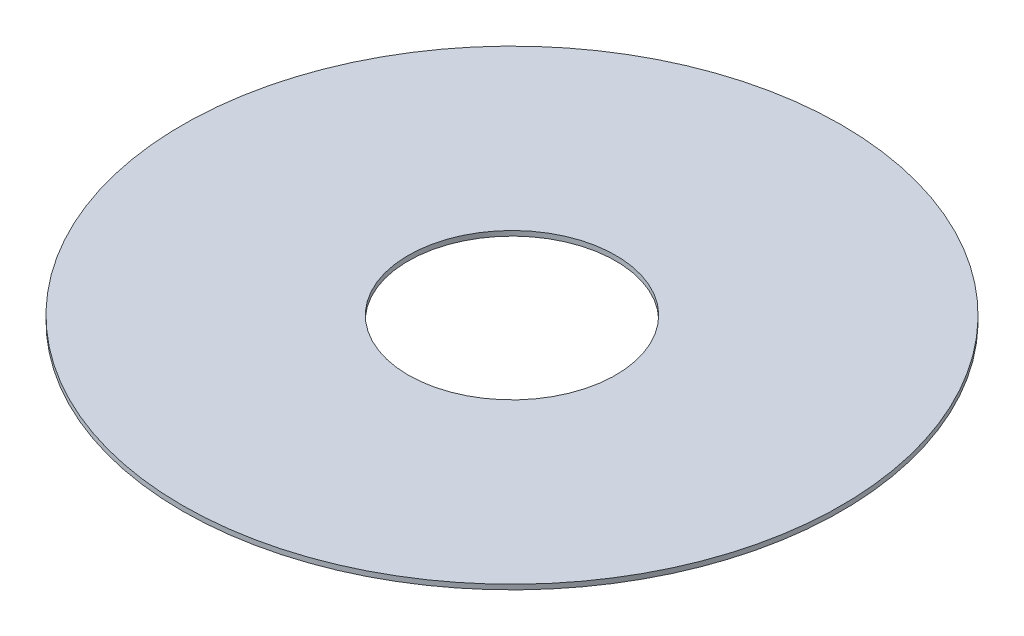
SolidWorks part; units mm, degrees
ref_plane "Front Plane" through (0, 0, 0) normal (0, 0, 1) x (1, 0, 0)
ref_plane "Top Plane" through (0, 0, 0) normal (0, 1, 0) x (1, 0, 0)
ref_plane "Right Plane" through (0, 0, 0) normal (1, 0, 0) x (0, 0, -1)
sketch "Sketch1" plane through (0, 0, 0) normal (0, 1, 0) x (1, 0, 0)
  circle A0 centre (0, 0) radius 34.29
  circle A1 centre (0, 0) radius 10.795
  dimension "D1" = 68.58
  dimension "D2" = 21.59
extrude "Boss-Extrude1" add sketch "Sketch1" along normal blind 0.508
